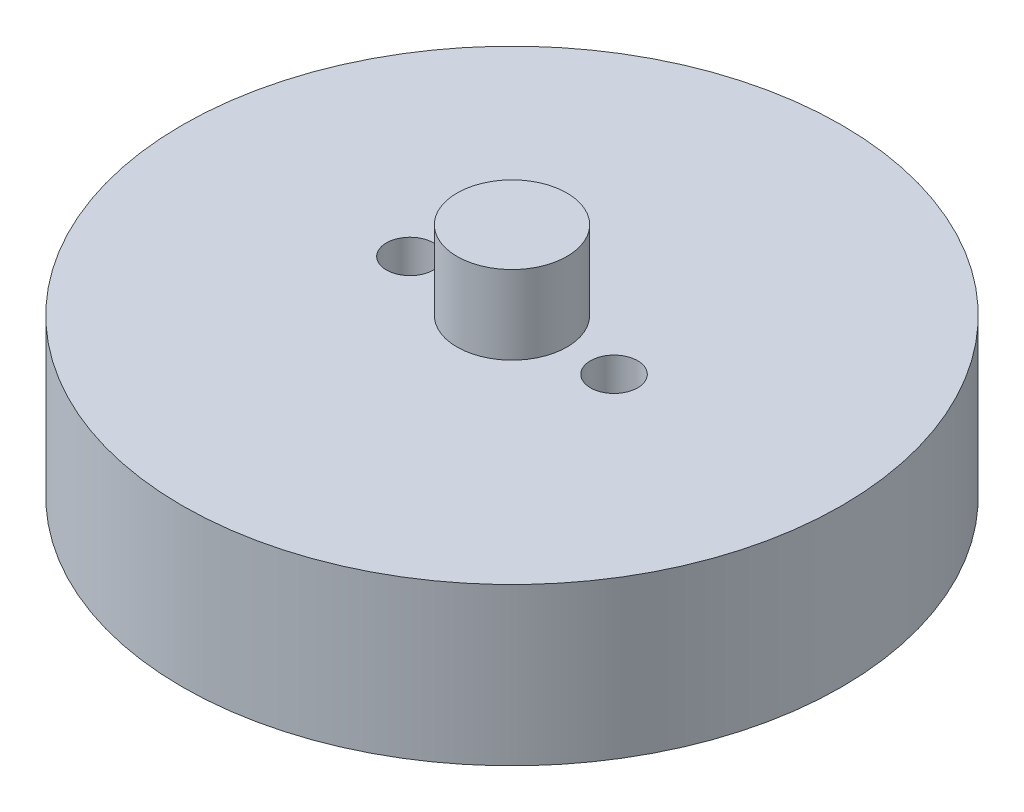
SolidWorks part; units mm, degrees
material "6061 合金"
ref_plane "前视基准面" through (0, 0, 0) normal (0, 0, 1) x (1, 0, 0)
ref_plane "上视基准面" through (0, 0, 0) normal (0, 1, 0) x (1, 0, 0)
ref_plane "右视基准面" through (0, 0, 0) normal (1, 0, 0) x (0, 0, -1)
sketch "草图1" plane through (0, 0, 0) normal (0, 1, 0) x (1, 0, 0)
  line L0 (-6.5, 0) -> (6.5, 0) construction
  circle A0 centre (0, 0) radius 21
  circle A1 centre (-6.5, 0) radius 1.5
  circle A2 centre (6.5, 0) radius 1.5
  dimension "D1" = 42
  dimension "D3" = 3
  dimension "D2" = 13
extrude "凸台-拉伸1" add sketch "草图1" along normal blind 10
sketch "草图2" plane through (0, 10, 0) normal (0, 1, 0) x (1, 0, 0)
  circle A0 centre (0, 0) radius 3.5
  dimension "D1" = 7
extrude "凸台-拉伸2" add sketch "草图2" along normal blind 5
